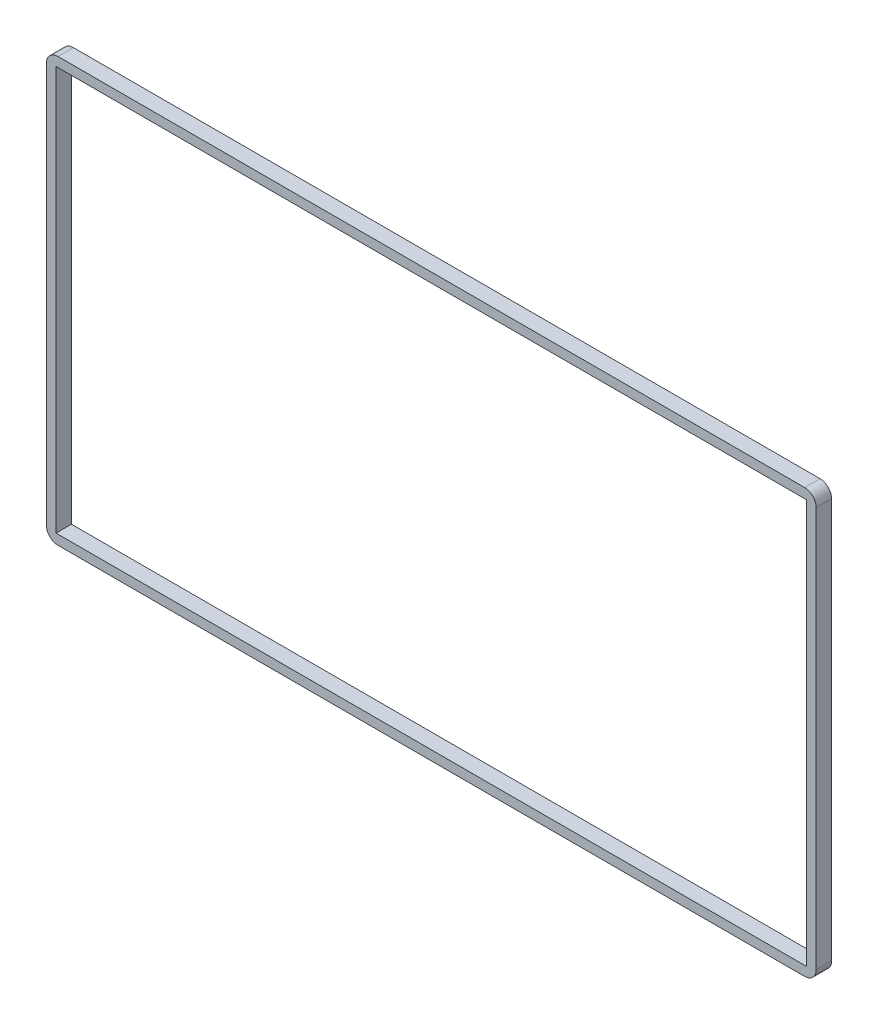
SolidWorks part; units mm, degrees
ref_plane "Front Plane" through (0, 0, 0) normal (0, 0, 1) x (1, 0, 0)
ref_plane "Top Plane" through (0, 0, 0) normal (0, 1, 0) x (1, 0, 0)
ref_plane "Right Plane" through (0, 0, 0) normal (1, 0, 0) x (0, 0, -1)
sketch "Sketch1" plane through (0, 0, 0) normal (0, 0, 1) x (1, 0, 0)
  line L0 (0, -15.0985) -> (0, -16.3485) construction
  line L1 (-37.897, -16.3485) -> (62.103, -16.3485)
  line L2 (-37.897, -16.3485) -> (-37.897, 38.6515)
  line L3 (-37.897, 38.6515) -> (62.103, 38.6515)
  line L4 (62.103, -16.3485) -> (62.103, 38.6515)
  line L5 (-36.647, 37.4015) -> (60.853, 37.4015)
  line L6 (-36.647, 37.4015) -> (-36.647, -15.0985)
  line L7 (-36.647, -15.0985) -> (60.853, -15.0985)
  line L8 (60.853, 37.4015) -> (60.853, -15.0985)
  line L9 (-36.647, 12.9892) -> (-37.897, 12.9892) construction
  line L10 (60.853, 11.7148) -> (62.103, 11.7148) construction
  line L11 (4.3602, 37.4015) -> (4.3602, 38.6515) construction
  dimension "D1" = 55
  dimension "D2" = 100
  dimension "D3" = 1.25
extrude "Boss-Extrude1" add sketch "Sketch1" along normal blind 2
fillet "Fillet1" radius 1.5 4 edges at (-37.897, -16.3485, 1) (62.103, -16.3485, 1) (62.103, 38.6515, 1) (-37.897, 38.6515, 1)
